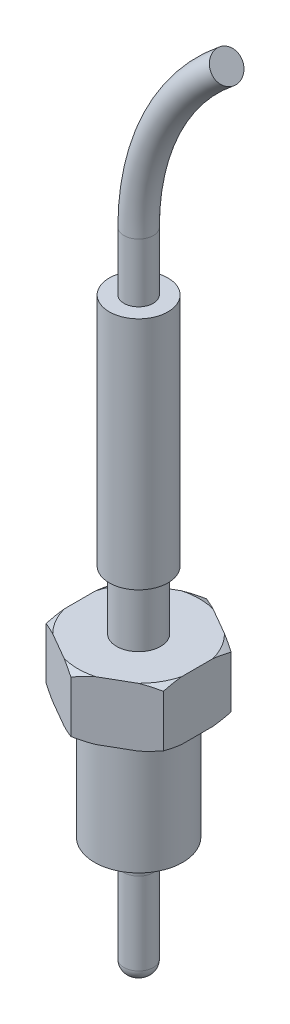
SolidWorks part; units mm, degrees
material "Alloy Steel (SS)"
ref_plane "Front Plane" through (0, 0, 0) normal (0, 0, 1) x (1, 0, 0)
ref_plane "Top Plane" through (0, 0, 0) normal (0, 1, 0) x (1, 0, 0)
ref_plane "Right Plane" through (0, 0, 0) normal (1, 0, 0) x (0, 0, -1)
sketch "Sketch1" plane through (0, 0, 0) normal (0, 0, 1) x (1, 0, 0)
  line L0 (0, 0) -> (0, 63.5)
  line L2 (2.3812, 38.1) -> (2.3812, 31.75)
  line L3 (2.3812, 31.75) -> (12.7, 31.75)
  line L4 (12.7, 31.75) -> (12.7, 25.4)
  line L5 (12.7, 25.4) -> (4.7625, 25.4)
  line L6 (4.7625, 25.4) -> (4.7625, 12.7)
  line L7 (4.7625, 12.7) -> (1.5875, 12.7)
  line L8 (1.5875, 12.7) -> (1.5875, 0)
  line L9 (1.5875, 0) -> (0, 0)
  line L10 (0, 0) -> (0, -5.7178) construction
  line L11 (2.3812, 38.1) -> (3.175, 38.1)
  line L12 (3.175, 38.1) -> (3.175, 63.5)
  line L13 (3.175, 63.5) -> (0, 63.5)
  point P15 (0, 43.1725)
  point P16 (-1.628, 42.5361)
  dimension "D1" = 3.175
  dimension "D2" = 9.525
  dimension "D3" = 25.4
  dimension "D4" = 12.7
  dimension "D5" = 12.7
  dimension "D6" = 6.35
  dimension "D7" = 6.35
  dimension "D8" = 4.7625
  dimension "D9" = 6.35
  dimension "D10" = 25.4
revolve "Revolve1" add sketch "Sketch1" angle 360 about L10
sketch "Sketch2" plane through (0, 0, 0) normal (0, 1, 0) x (1, 0, 0)
  line L1 (6.35, 3.6662) -> (0, 7.3323)
  line L2 (0, 7.3323) -> (-6.35, 3.6662)
  line L3 (-6.35, 3.6662) -> (-6.35, -3.6662)
  line L4 (-6.35, -3.6662) -> (0, -7.3323)
  line L5 (0, -7.3323) -> (6.35, -3.6662)
  line L6 (6.35, -3.6662) -> (6.35, 3.6662)
  circle A0 centre (0, 0) radius 6.35 construction
  dimension "D1" = 12.7
extrude "Cut-Extrude1" cut sketch "Sketch2" along normal through all flip side to cut
sketch "Sketch3" plane through (0, 0, 0) normal (1, 0, 0) x (0, 0, -1)
  line L0 (7.3323, 28.575) -> (17.5459, 28.575) construction
  line L1 (7.3323, 31.75) -> (7.3323, 25.4) construction
  line L2 (3.6662, 31.75) -> (7.3323, 31.75) construction
  line L3 (7.3323, 31.369) -> (7.3323, 25.781)
  line L4 (0, 0) -> (0, 63.5) construction
  line L5 (3.175, 63.5) -> (-3.175, 63.5) construction
  arc A0 (6.5703, 31.75) -> (7.3323, 31.369) centre (1.2749, 20.2067) cw
  arc A1 (6.5703, 31.75) -> (17.5459, 28.575) centre (9.8015, 22.3616) cw
  arc A2 (6.5703, 25.4) -> (7.3323, 25.781) centre (1.2749, 36.9433) ccw
  arc A3 (6.5703, 25.4) -> (17.5459, 28.575) centre (9.8015, 34.7884) ccw
  point P10 (7.3323, 28.575)
  dimension "D1" = 12.7
  dimension "D2" = 0.381
  dimension "D3" = 0.762
revolve "Cut-Revolve1" cut sketch "Sketch3" angle 360 about L4
fillet "Fillet1" radius 2.54 1 edges at (0, 12.7, 1.5875)
fillet "Fillet2" radius 1.27 1 edges at (0, 0, 1.5875)
sketch "Sketch4" plane through (0, 0, 0) normal (0, 0, 1) x (1, 0, 0)
  line L0 (0, 63.5) -> (0, 69.85)
  line L1 (3.175, 63.5) -> (-3.175, 63.5) construction
  arc A0 (0, 69.85) -> (9.525, 89.6779) centre (25.4, 69.85) cw
  point P5 (0, 63.5)
  dimension "D1" = 6.35
  dimension "D2" = 25.4
  dimension "D3" = 9.525
sweep "Sweep1" add path "Sketch4" circular profile diameter 3.175 parameters "D3"=3.175
